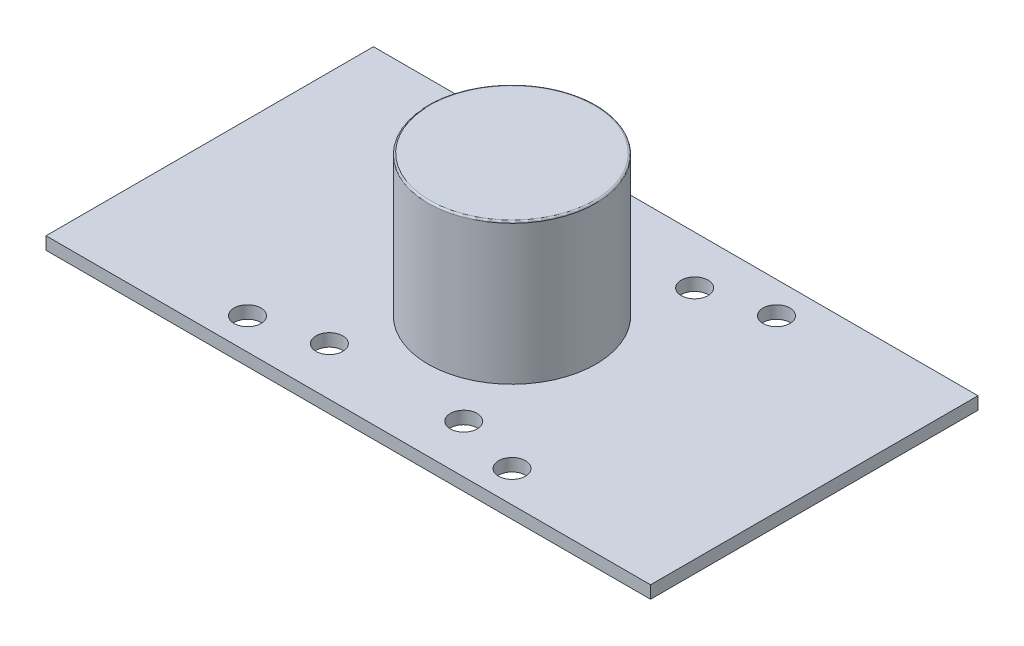
SolidWorks part; units mm, degrees
ref_plane "Front Plane" through (0, 0, 0) normal (0, 0, 1) x (1, 0, 0)
ref_plane "Top Plane" through (0, 0, 0) normal (0, 1, 0) x (1, 0, 0)
ref_plane "Right Plane" through (0, 0, 0) normal (1, 0, 0) x (0, 0, -1)
sketch "Sketch1" plane through (0, 0, 0) normal (0, 1, 0) x (1, 0, 0)
  line L0 (0, 0) -> (72, 0)
  line L1 (72, 0) -> (72, 39)
  line L2 (72, 39) -> (0, 39)
  line L3 (0, 39) -> (0, 0)
extrude "Boss-Extrude1" add sketch "Sketch1" along normal blind 1.5
sketch "Sketch2" plane through (0, 1.5, 0) normal (0, 1, 0) x (1, 0, 0)
  circle A0 centre (36, 19.5) radius 10
extrude "Boss-Extrude2" add sketch "Sketch2" along normal blind 16.8
sketch "Sketch3" plane through (0, 1.5, 0) normal (0, 1, 0) x (1, 0, 0)
  circle A0 centre (44, 5.75) radius 1.6
  circle A1 centre (28, 5.75) radius 1.6
  circle A2 centre (28, 33.25) radius 1.6
  circle A3 centre (44, 33.25) radius 1.6
  point P0 (0, 0)
extrude "Cut-Extrude1" cut sketch "Sketch3" against normal blind 16.8
sketch "Sketch4" plane through (0, 1.5, 0) normal (0, 1, 0) x (1, 0, 0)
  circle A0 centre (51.75, 3.75) radius 1.6
  circle A1 centre (51.75, 35.25) radius 1.6
  circle A2 centre (20.25, 3.75) radius 1.6
  circle A3 centre (20.25, 35.25) radius 1.6
extrude "Cut-Extrude2" cut sketch "Sketch4" against normal blind 16.8
fillet "Fillet1" radius 0.2 1 edges at (36, 18.3, -9.5)
